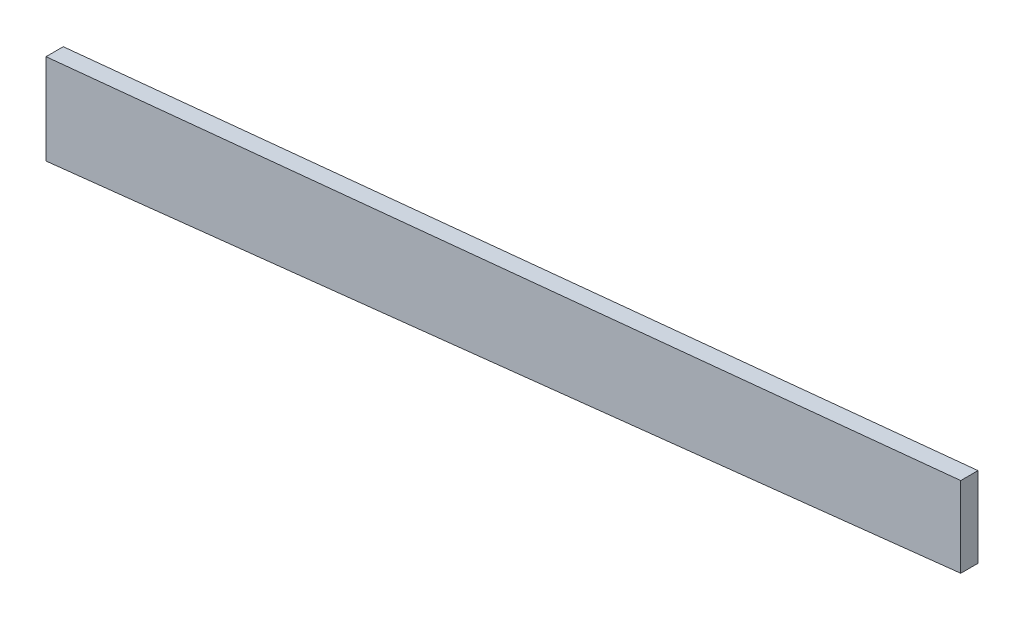
SolidWorks part; units mm, degrees
ref_plane "Front Plane" through (0, 0, 0) normal (0, 0, 1) x (1, 0, 0)
ref_plane "Top Plane" through (0, 0, 0) normal (0, 1, 0) x (1, 0, 0)
ref_plane "Right Plane" through (0, 0, 0) normal (1, 0, 0) x (0, 0, -1)
sketch "Sketch1" plane through (0, 0, 0) normal (0, 0, 1) x (1, 0, 0)
  line L0 (-1.5875, 124.3502) -> (-169.8625, 105.8906)
  line L1 (-1.5875, 139.1271) -> (-169.8625, 122.5198)
  line L8 (-1.5875, 139.1271) -> (-1.5875, 124.3502)
  line L9 (-1.5875, 124.3502) -> (1.5875, 124.356)
  line L10 (1.5875, 124.356) -> (1.5875, 139.1271)
  line L11 (1.5875, 139.1271) -> (-1.5875, 139.1271)
  line L16 (-173.0375, 122.5198) -> (-173.0375, 105.8852)
  line L17 (-173.0375, 105.8852) -> (-169.8625, 105.8906)
  line L18 (-169.8625, 105.8906) -> (-169.8625, 122.5198)
  line L19 (-169.8625, 122.5198) -> (-173.0375, 122.5198)
extrude "Boss-Extrude1" add sketch "Sketch1" against normal blind 3.175 contours L18 L0 L8 L1
